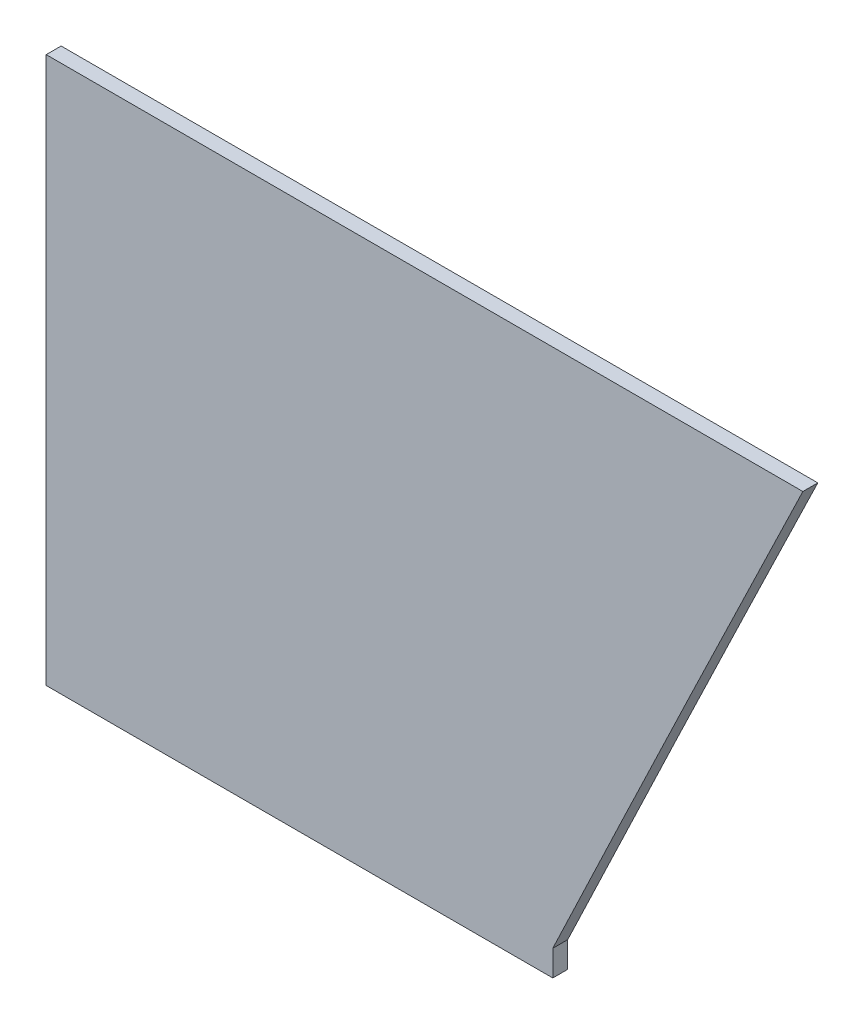
SolidWorks part; units mm, degrees
ref_plane "Front Plane" through (0, 0, 0) normal (0, 0, 1) x (1, 0, 0)
ref_plane "Top Plane" through (0, 0, 0) normal (0, 1, 0) x (1, 0, 0)
ref_plane "Right Plane" through (0, 0, 0) normal (1, 0, 0) x (0, 0, -1)
sketch "Sketch1" plane through (0, 0, 0) normal (0, 0, 1) x (1, 0, 0)
  line L0 (257.5483, 177.2093) -> (-257.5481, 177.2094)
  line L1 (-257.5481, 177.2094) -> (-257.5482, -177.2093)
  line L2 (-257.5482, -177.2093) -> (87.3055, -177.2094) construction
  line L3 (-257.5482, -177.2093) -> (-257.5482, -194.7353)
  line L4 (-257.5482, -194.7353) -> (87.3055, -194.7353)
  line L5 (87.3055, -194.7353) -> (87.3055, -177.2094)
  spline S0 degree 3 poles (87.3055, -177.2094) (115.4437, -118.0267) (143.6931, -58.8973) (200.4351, 59.2453) (228.9283, 118.2581) (257.5483, 177.2093) knots 0 0 0 0 0.5 0.5 1 1 1 1
  dimension "D1" = 354.4187
  dimension "D2" = 17.526
  dimension "D3" = 344.8537
extrude "Boss-Extrude2" add sketch "Sketch1" along normal blind 10.16
